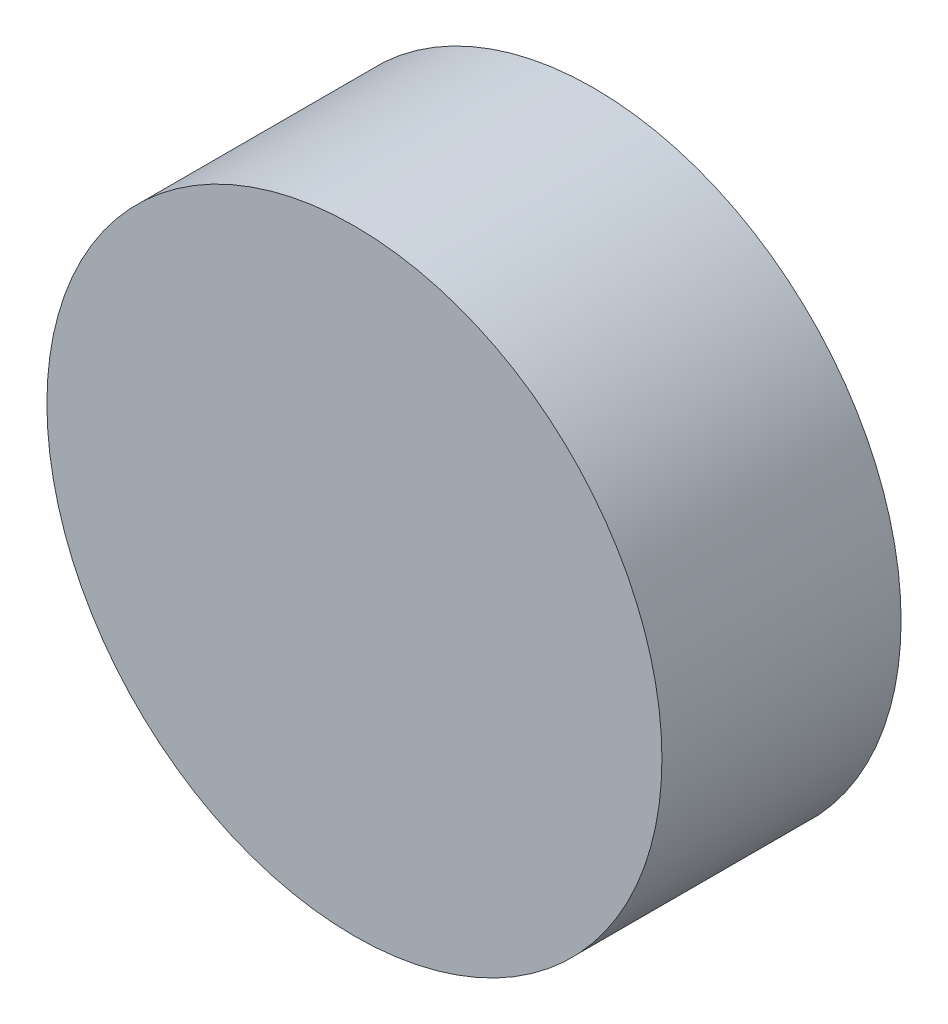
SolidWorks part; units mm, degrees
ref_plane "Front Plane" through (0, 0, 0) normal (0, 0, 1) x (1, 0, 0)
ref_plane "Top Plane" through (0, 0, 0) normal (0, 1, 0) x (1, 0, 0)
ref_plane "Right Plane" through (0, 0, 0) normal (1, 0, 0) x (0, 0, -1)
sketch "Sketch1" plane through (0, 0, 0) normal (0, 0, 1) x (1, 0, 0)
  circle A0 centre (-14.1465, 25.0616) radius 9
  point P2 (-152.0542, -6.9887)
extrude "Boss-Extrude3" add sketch "Sketch1" along normal blind 7
